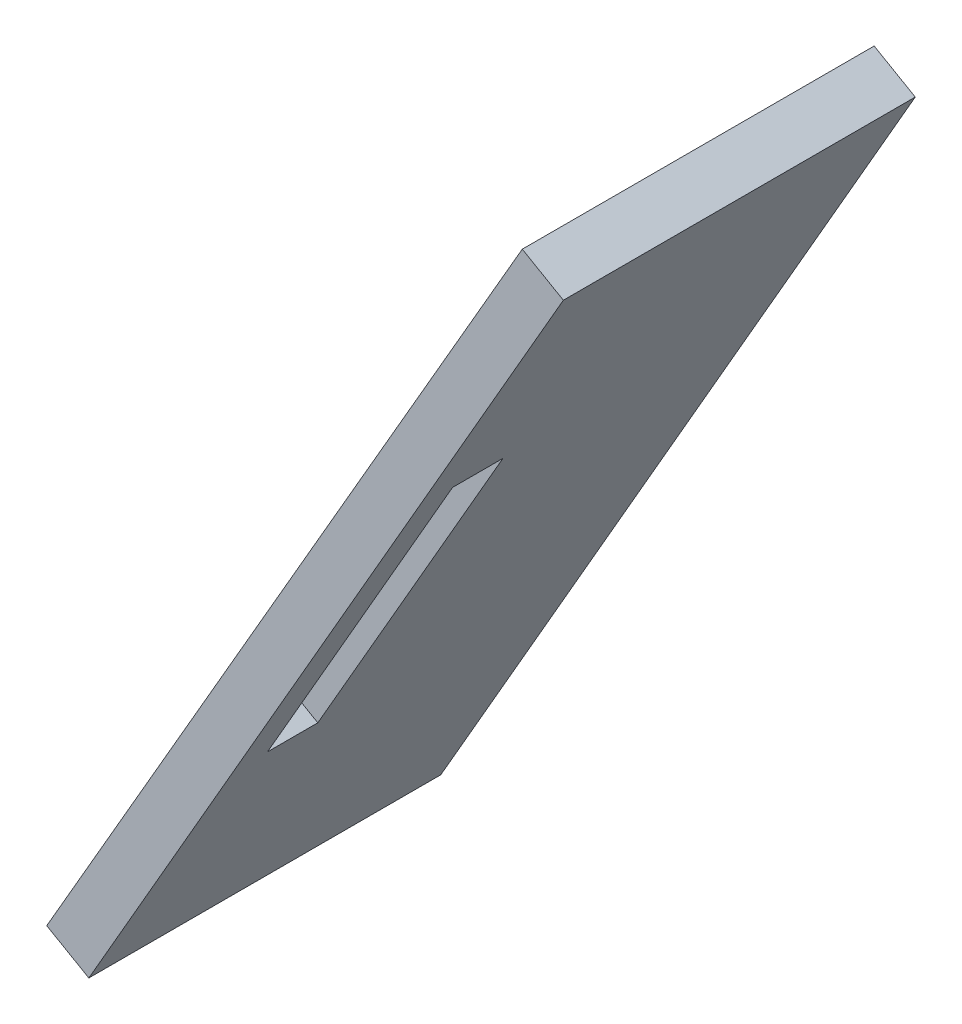
SolidWorks part; units mm, degrees
ref_plane "Alzado" through (0, 0, 0) normal (0, 0, 1) x (1, 0, 0)
ref_plane "Planta" through (0, 0, 0) normal (0, 1, 0) x (1, 0, 0)
ref_plane "Vista lateral" through (0, 0, 0) normal (1, 0, 0) x (0, 0, -1)
sketch "Croquis1" plane through (0, 0, 0) normal (0, 0, 1) x (1, 0, 0)
  line L0 (50, -86.6025) -> (54.4277, -89.1516)
  line L1 (58.0648, -82.8338) -> (52.959, -91.7025) construction
  line L2 (54.4277, -89.1516) -> (104.3209, -2.4875)
  line L3 (104.3209, -2.4875) -> (100, 0)
  line L4 (100, 0) -> (50, -86.6025)
extrude "Saliente-Extruir1" add sketch "Croquis1" along normal up to surface (37 mm away)
sketch "Croquis2" plane through (79.4275, -45.7271, 0) normal (0.8666, -0.4989, 0) x (0, 0, -1)
  line L0 (-33.2244, -0.1362) -> (-33.4244, -0.1362)
  line L1 (-33.2244, 14.8133) -> (-33.2244, -15.0856) construction
  line L2 (-33.4244, 19.3729) -> (-33.4244, -19.6452)
  line L3 (-33.4244, -19.6452) -> (-28.1244, -19.6452)
  line L4 (-28.1244, -19.6452) -> (-28.1244, 19.3729)
  line L5 (-33.4244, 19.3729) -> (-28.1244, 19.3729)
  point P8 (-28.1244, -0.1362)
extrude "Cortar-Extruir1" cut sketch "Croquis2" against normal blind 10
